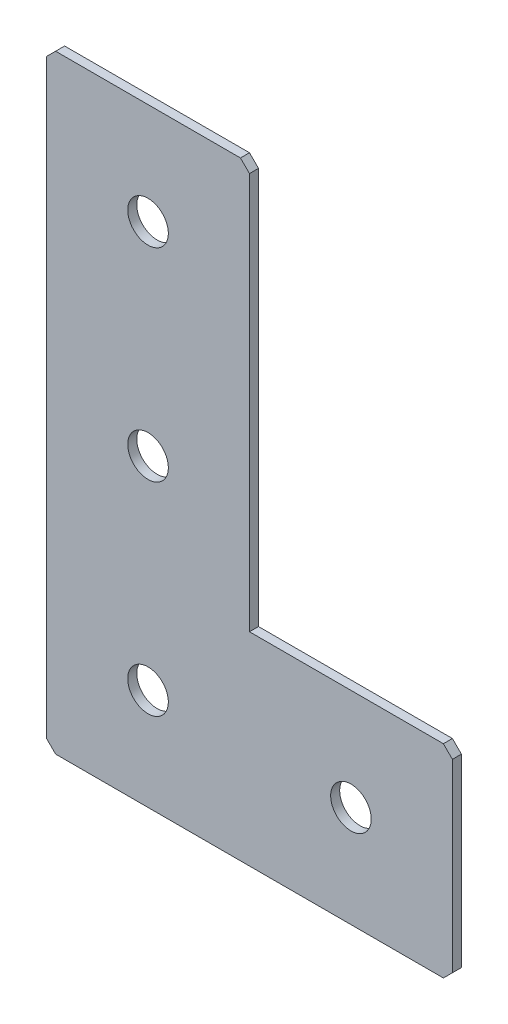
SolidWorks part; units mm, degrees
material "Простая углеродистая сталь"
ref_plane "Спереди(Плоскость XY)" through (0, 0, 0) normal (0, 0, 1) x (1, 0, 0)
ref_plane "Сверху(Плоскость XZ)" through (0, 0, 0) normal (0, 1, 0) x (1, 0, 0)
ref_plane "Справа(Плоскость ZY)" through (0, 0, 0) normal (1, 0, 0) x (0, 0, -1)
sketch "Эскиз1" plane through (0, 0, 0) normal (0, 0, -1) x (1, 0, 0)
  line L0 (0, 0) -> (0, 135)
  line L1 (0, 135) -> (90, 135)
  line L2 (90, 135) -> (90, 90)
  line L3 (90, 90) -> (45, 90)
  line L4 (45, 90) -> (45, 0)
  line L5 (45, 0) -> (0, 0)
  dimension "D1" = 135
  dimension "D3" = 45
extrude "Бобышка-Вытянуть1" add sketch "Эскиз1" along normal blind 2
hole_wizard "Отверстие с зазором M81" positions "Эскиз2" profile "Эскиз3" hole size "M8" standard "DIN" end condition through all
sketch "Эскиз2" plane through (0, 0, -2) normal (0, 0, -1) x (1, 0, 0)
  line L1 (0, 0) -> (45, 0) construction
  line L7 (22.5, 0) -> (22.5, 22.5) construction
  line L9 (90, 90) -> (90, 135) construction
  point P0 (67.5, 112.5)
  point P2 (22.5, 112.5)
  point P4 (22.5, 67.5)
  point P6 (22.5, 22.5)
  dimension "D1" = 45
  dimension "D2" = 45
  dimension "D3" = 45
  dimension "D4" = 22.5
  dimension "D5" = 22.5
sketch "Эскиз3" plane through (67.5, -112.5, -2) normal (1, 0, 0) x (0, 1, 0)
  line L0 (0, 0) -> (0, 2)
  line L1 (0, 2) -> (4.5, 2)
  line L2 (4.5, 2) -> (4.5, 0)
  line L5 (4.5, 0) -> (0, 0)
  line L11 (0, -6.35) -> (0, 107.95) construction
  dimension "Диаметр сквозного отверстия" = 9
  dimension "Глубина сквозного отверстия" = 2
chamfer "Фаска1" distance 2 angle 45 5 edges at (0, 0, -1) (45, 0, -1) (90, -90, -1) (90, -135, -1) (0, -135, -1)
